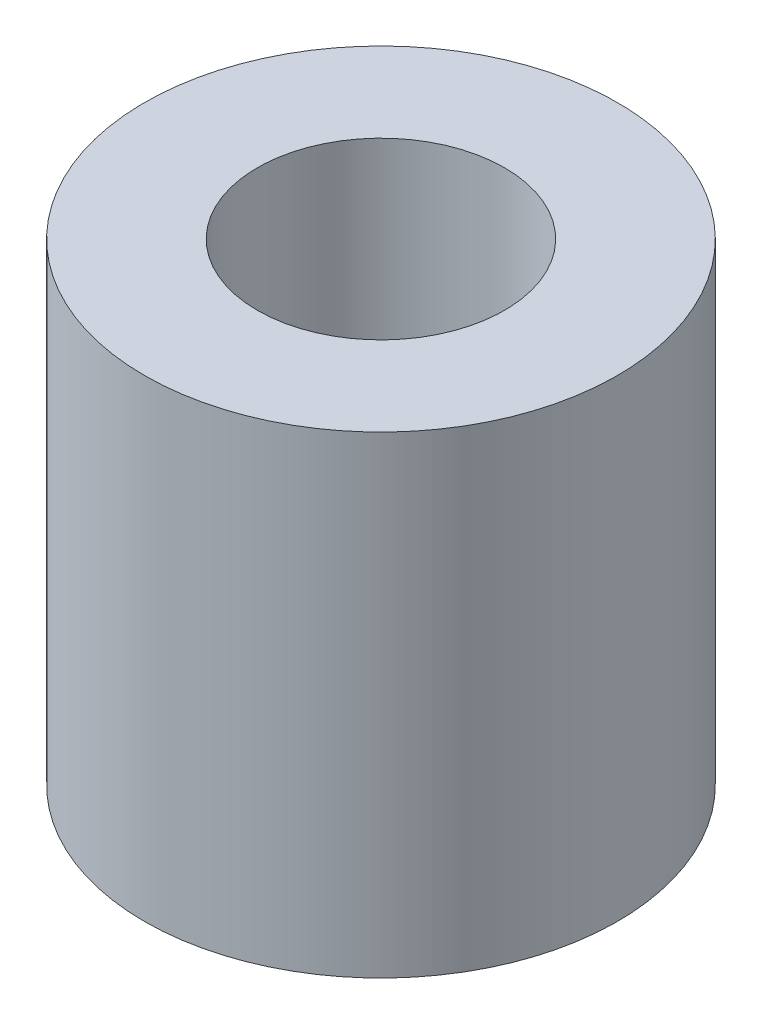
SolidWorks part; units mm, degrees
material "6061 Alloy"
ref_plane "Front Plane" through (0, 0, 0) normal (0, 0, 1) x (1, 0, 0)
ref_plane "Top Plane" through (0, 0, 0) normal (0, 1, 0) x (1, 0, 0)
ref_plane "Right Plane" through (0, 0, 0) normal (1, 0, 0) x (0, 0, -1)
sketch "Sketch1" plane through (0, 0, 0) normal (0, 1, 0) x (1, 0, 0)
  circle A0 centre (0, 0) radius 2.4892
  circle A1 centre (0, 0) radius 4.7625
  dimension "D1" = 4.9784
  dimension "D2" = 9.525
extrude "Boss-Extrude1" add sketch "Sketch1" along normal blind 9.525
